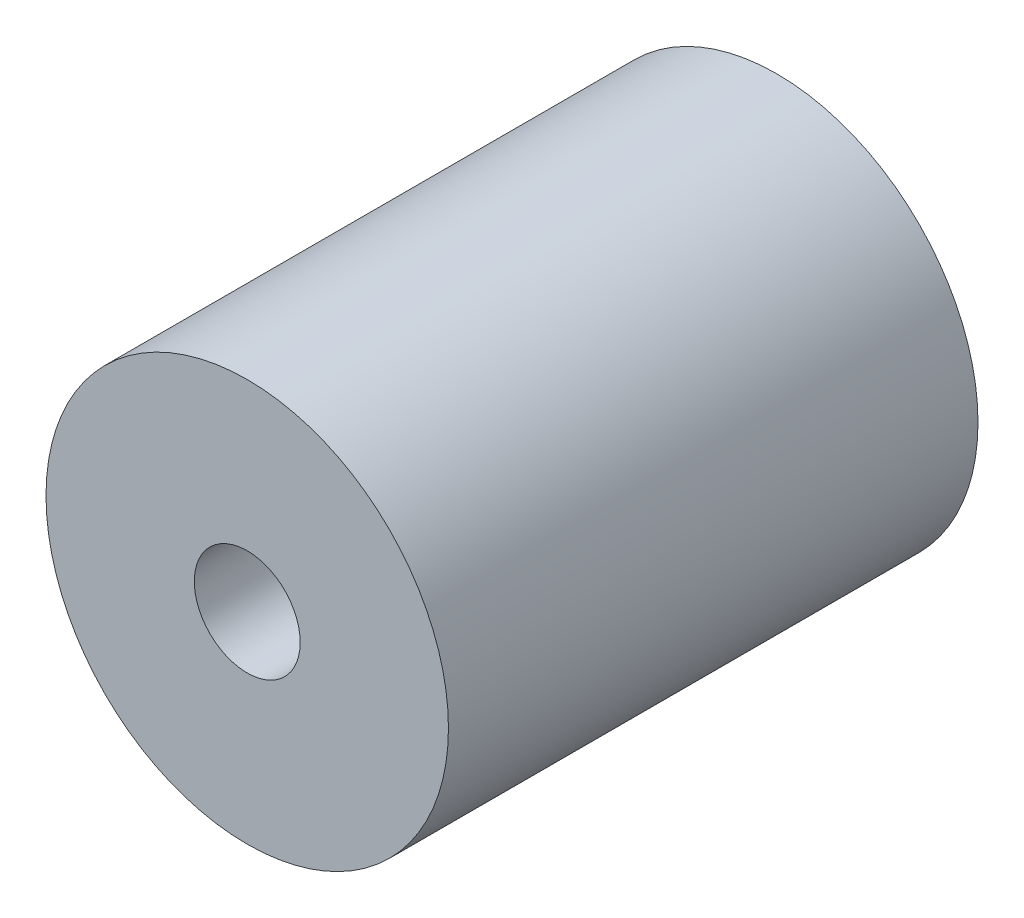
SolidWorks part; units mm, degrees
ref_plane "前视基准面" through (0, 0, 0) normal (0, 0, 1) x (1, 0, 0)
ref_plane "上视基准面" through (0, 0, 0) normal (0, 1, 0) x (1, 0, 0)
ref_plane "右视基准面" through (0, 0, 0) normal (1, 0, 0) x (0, 0, -1)
ref_plane "基准面1" through (0, 0, 10) normal (0, 0, 1) x (1, 0, 0)
sketch "草图2" plane through (0, 0, 10) normal (0, 0, 1) x (1, 0, 0)
  circle A0 centre (-14.7886, 7.4927) radius 9.5
  dimension "D1" = 19
extrude "凸台-拉伸1" add sketch "草图2" along normal mid plane 25
sketch "草图4" plane through (0, 0, 10) normal (0, 0, 1) x (1, 0, 0)
  circle A0 centre (-14.7886, 7.4927) radius 4
  circle A1 centre (-14.7886, 7.4927) radius 9.5 construction
  circle A2 centre (-14.7886, 7.4927) radius 9.5
extrude "切除-拉伸1" cut sketch "草图4" against normal blind 12.5 flip side to cut
sketch "草图5" plane through (0, 0, 10) normal (0, 0, 1) x (1, 0, 0)
  circle A0 centre (-14.7886, 7.4927) radius 9.5 construction
  circle A1 centre (-14.7886, 7.4927) radius 9.5
  circle A2 centre (-14.7886, 7.4927) radius 2.5
extrude "切除-拉伸2" cut sketch "草图5" along normal blind 12.5 flip side to cut
